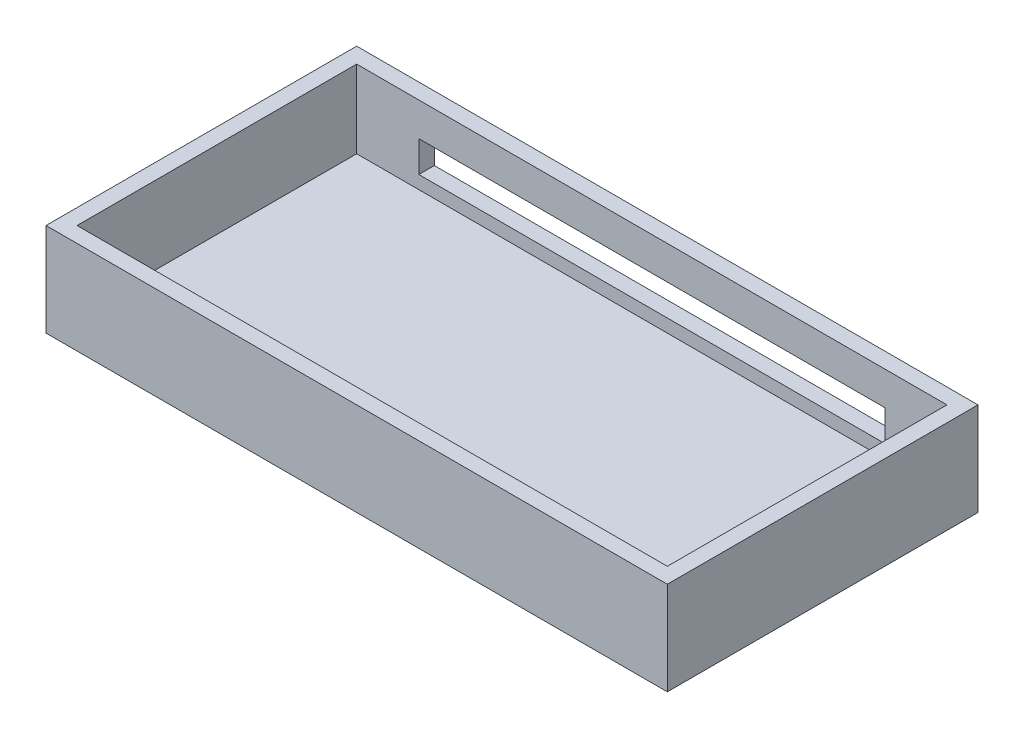
SolidWorks part; units mm, degrees
ref_plane "Front Plane" through (0, 0, 0) normal (0, 0, 1) x (1, 0, 0)
ref_plane "Top Plane" through (0, 0, 0) normal (0, 1, 0) x (1, 0, 0)
ref_plane "Right Plane" through (0, 0, 0) normal (1, 0, 0) x (0, 0, -1)
sketch "Sketch2" plane through (0, 0, 0) normal (0, 1, 0) x (1, 0, 0)
  line L1 (-100, 50) -> (100, 50)
  line L2 (-100, 50) -> (-100, -50)
  line L3 (-100, -50) -> (100, -50)
  line L4 (100, 50) -> (100, -50)
  line L5 (-100, 50) -> (100, -50) construction
  line L6 (-100, -50) -> (100, 50) construction
  point P0 (0, 0)
  dimension "D1" = 200
  dimension "D2" = 100
extrude "Boss-Extrude1" add sketch "Sketch2" along normal blind 30
shell "Shell1" thickness 5
sketch "Sketch3" plane through (0, 0, -45) normal (0, 0, 1) x (1, 0, 0)
  line L0 (95, 30) -> (95, 5) construction
  line L1 (-75, 19.2236) -> (75, 19.2236)
  line L2 (-75, 19.2236) -> (-75, 9.2236)
  line L3 (-75, 9.2236) -> (75, 9.2236)
  line L4 (75, 19.2236) -> (75, 9.2236)
  line L5 (-75, 19.2236) -> (75, 9.2236) construction
  line L6 (-75, 9.2236) -> (75, 19.2236) construction
  line L7 (-95, 30) -> (-95, 5) construction
  point P0 (0, 14.2236)
  dimension "D1" = 20
  dimension "D2" = 10
  dimension "D3" = 20
extrude "Cut-Extrude1" cut sketch "Sketch3" against normal blind 10
